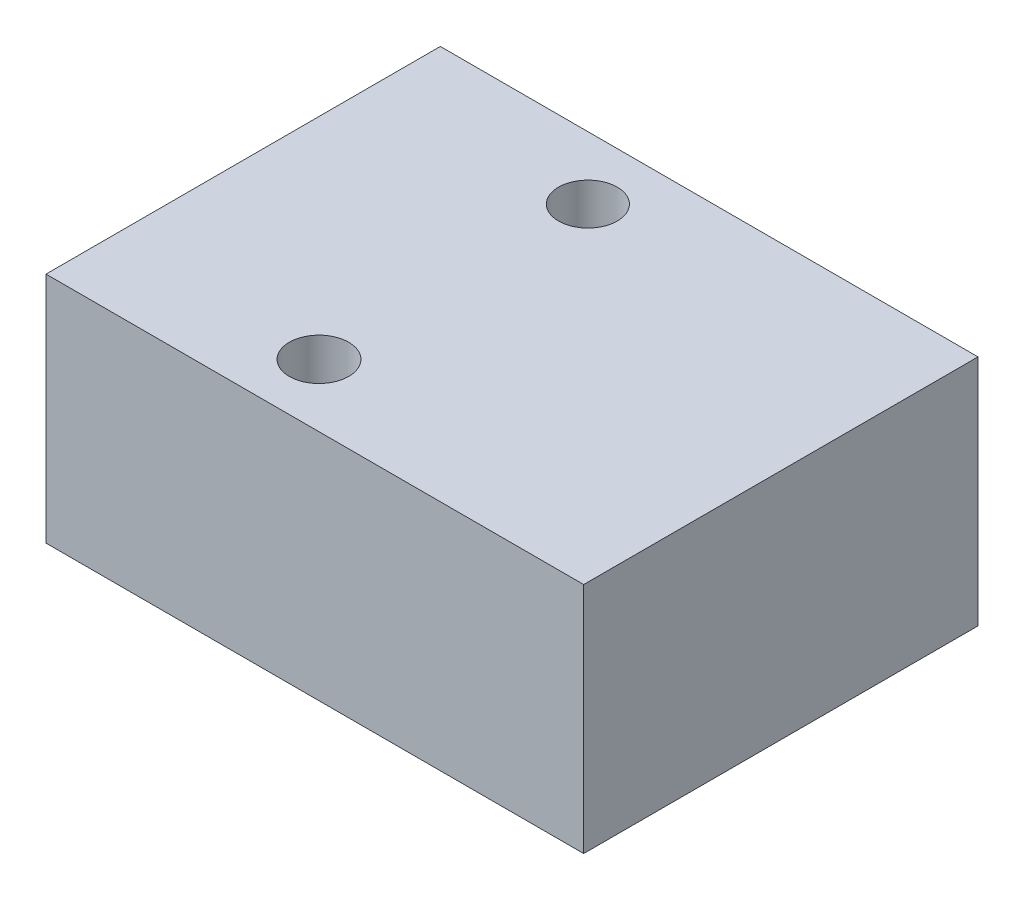
SolidWorks part; units mm, degrees
ref_plane "Płaszczyzna przednia" through (0, 0, 0) normal (0, 0, 1) x (1, 0, 0)
ref_plane "Płaszczyzna górna" through (0, 0, 0) normal (0, 1, 0) x (1, 0, 0)
ref_plane "Płaszczyzna prawa" through (0, 0, 0) normal (1, 0, 0) x (0, 0, -1)
sketch "Sketch1" plane through (0, 0, 0) normal (0, 1, 0) x (1, 0, 0)
  line L1 (-15, -7.4018) -> (15, -7.4018)
  line L2 (-15, -7.4018) -> (-15, 14.5982)
  line L3 (-15, 14.5982) -> (15, 14.5982)
  line L4 (15, -7.4018) -> (15, 14.5982)
  dimension "D1" = 30
  dimension "D2" = 22
extrude "Boss-Extrude1" add sketch "Sketch1" along normal blind 13
sketch "Sketch2" plane through (0, 13, 0) normal (0, 1, 0) x (1, 0, 0)
  circle A0 centre (-3.2653, 11.0972) radius 1.6396
  circle A1 centre (-3.2653, -3.9052) radius 1.6558
extrude "Cut-Extrude1" cut sketch "Sketch2" against normal blind 20
